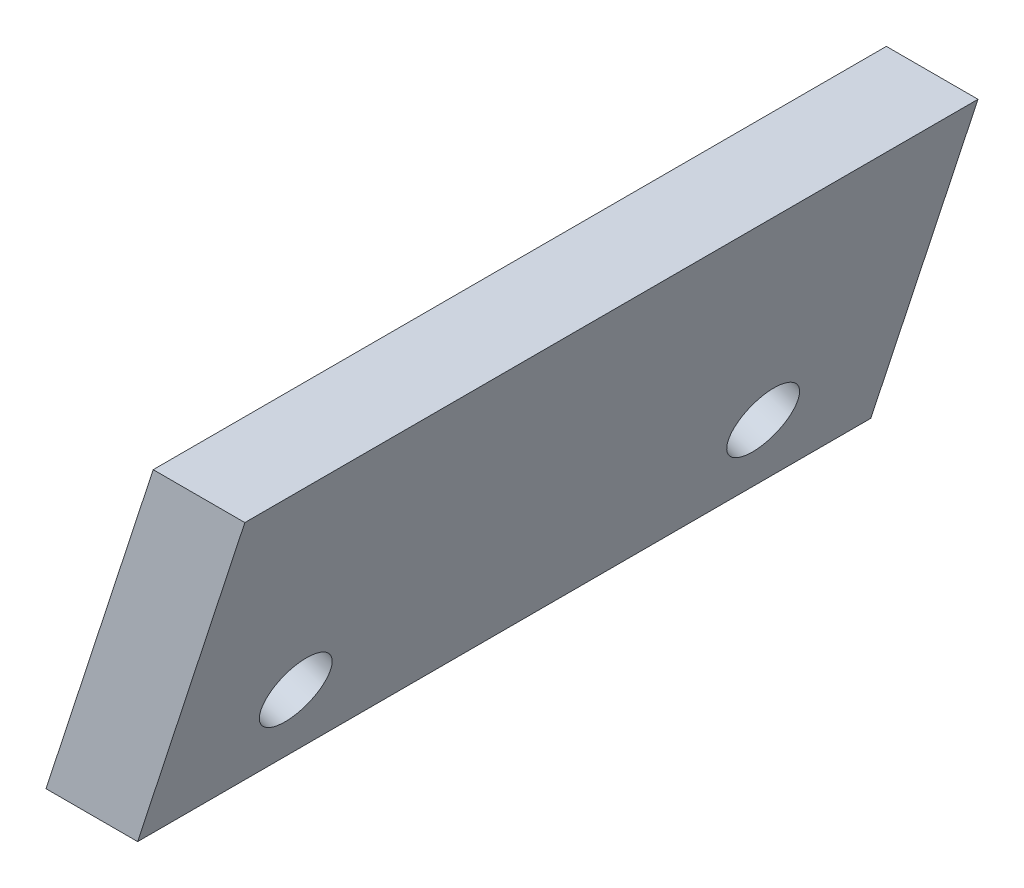
SolidWorks part; units mm, degrees
ref_plane "Front Plane" through (0, 0, 0) normal (0, 0, 1) x (1, 0, 0)
ref_plane "Top Plane" through (0, 0, 0) normal (0, 1, 0) x (1, 0, 0)
ref_plane "Right Plane" through (0, 0, 0) normal (1, 0, 0) x (0, 0, -1)
sketch "Sketch2" plane through (0, 0, 0) normal (0, 0, 1) x (1, 0, 0)
  line L0 (0, 0) -> (2.5, 0)
  line L1 (0, 0) -> (2.9243, 9)
  line L2 (2.5, 0) -> (5.4243, 9)
  line L3 (5.4243, 9) -> (2.9243, 9)
  line L4 (2.5, 0) -> (7.5011, 0) construction
  dimension "D1" = 9
  dimension "D2" = 2.5
  dimension "D3" = 72
extrude "Boss-Extrude2" add sketch "Sketch2" along normal blind 20
sketch "Sketch4" plane through (0, 0, 0) normal (-0.9511, 0.309, 0) x (0, 0, 1)
  line L0 (0, 9.4632) -> (0, 0) construction
  line L1 (20, 9.4632) -> (20, 0) construction
  line L2 (20, 0) -> (0, 0) construction
  circle A0 centre (3.625, 3) radius 0.95
  circle A1 centre (16.375, 3) radius 0.95
  dimension "D1" = 3.625
  dimension "D2" = 3.625
  dimension "D3" = 3
  dimension "D4" = 3
  dimension "D5" = 1.9
  dimension "D6" = 1.9
extrude "Cut-Extrude1" cut sketch "Sketch4" against normal through all
